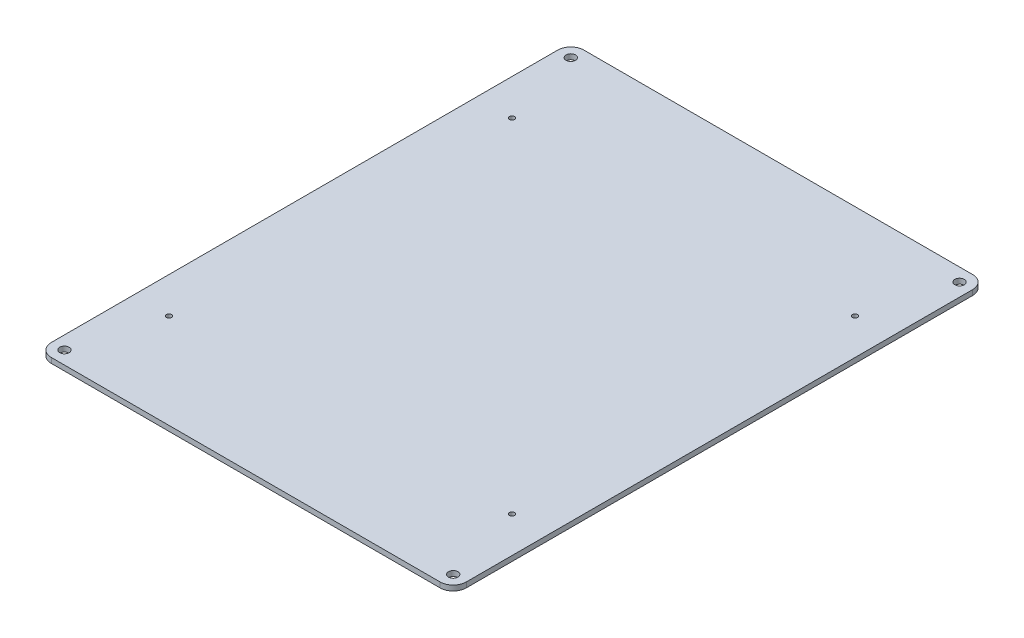
SolidWorks part; units mm, degrees
material "5052-H32"
ref_plane "Front Plane" through (0, 0, 0) normal (0, 0, 1) x (1, 0, 0)
ref_plane "Top Plane" through (0, 0, 0) normal (0, 1, 0) x (1, 0, 0)
ref_plane "Right Plane" through (0, 0, 0) normal (1, 0, 0) x (0, 0, -1)
sketch "Sketch1" plane through (0, 0, 0) normal (0, 1, 0) x (1, 0, 0)
  line L1 (127, 163) -> (-127, 163)
  line L2 (127, 163) -> (127, -163)
  line L3 (127, -163) -> (-127, -163)
  line L4 (-127, 163) -> (-127, -163)
  line L5 (0, -163) -> (0, 163) construction
  line L6 (127, 0) -> (-127, 0) construction
  point P0 (0, 0)
  dimension "D1" = 254
  dimension "D2" = 326
extrude "Boss-Extrude1" add sketch "Sketch1" along normal blind 3.175
sketch "Sketch2" plane through (0, 3.175, 0) normal (0, 1, 0) x (1, 0, 0)
  line L1 (105, 105) -> (-105, 105) construction
  line L2 (105, 105) -> (105, -105) construction
  line L3 (105, -105) -> (-105, -105) construction
  line L4 (-105, 105) -> (-105, -105) construction
  line L5 (0, -105) -> (0, 105) construction
  line L6 (105, 0) -> (-105, 0) construction
  point P4 (-105, 105)
  point P6 (-105, -105)
  point P7 (105, -105)
  point P8 (105, 105)
  dimension "D1" = 210
  dimension "D2" = 210
hole_wizard "M2.5 Clearance Hole1" positions "3DSketch1" profile "Sketch3" hole size "M2.5" standard "ANSI Metric"
sketch3d "3DSketch1"
  point P0 (-105, 3.175, 105)
  point P3 (-105, 3.175, -105)
  point P6 (105, 3.175, -105)
  point P9 (105, 3.175, 105)
sketch "Sketch3" plane through (-105, 3.175, 105) normal (1, 0, 0) x (0, 0, 1)
  line L0 (0, 0) -> (0, 12.8693)
  line L1 (0, 12.8693) -> (1.55, 11.938)
  line L2 (1.55, 11.938) -> (1.55, 0)
  line L5 (1.55, 0) -> (0, 0)
  line L10 (0, 12.8693) -> (-1.55, 11.938) construction
  line L11 (0, -6.35) -> (0, 107.95) construction
  dimension "Hole Dia." = 3.1
  dimension "Hole Depth" = 11.938
  dimension "Drill Angle" = 118
hole_wizard "M5 Clearance Hole1" positions "Sketch5" profile "Sketch4" hole size "M5" standard "ANSI Metric"
sketch "Sketch5" plane through (0, 3.175, 0) normal (0, 1, 0) x (1, 0, 0)
  line L0 (-119, 155) -> (119, -155) construction
  point P0 (-119, 155)
  point P2 (119, 155)
  point P4 (119, -155)
  point P6 (-119, -155)
  dimension "D1" = 238
  dimension "D2" = 310
sketch "Sketch4" plane through (-119, 3.175, -155) normal (1, 0, 0) x (0, 0, 1)
  line L0 (0, 0) -> (0, 13.6805)
  line L1 (0, 13.6805) -> (2.9, 11.938)
  line L2 (2.9, 11.938) -> (2.9, 0)
  line L5 (2.9, 0) -> (0, 0)
  line L10 (0, 13.6805) -> (-2.9, 11.938) construction
  line L11 (0, -6.35) -> (0, 107.95) construction
  dimension "Hole Dia." = 5.8
  dimension "Hole Depth" = 11.938
  dimension "Drill Angle" = 118
fillet "Fillet1" radius 8 4 edges at (127, 1.5875, -163) (-127, 1.5875, -163) (-127, 1.5875, 163) (127, 1.5875, 163)
sketch "Sketch6" plane through (0, 0, 0) normal (0, -1, 0) x (1, 0, 0)
  line L0 (-119, 163) -> (-342.6068, 163)
  line L1 (119, -163) -> (111.8034, -163)
  line L38 (127, -155) -> (127, -135)
  line L39 (127, -135) -> (119, -135)
  line L40 (119, -135) -> (119, -145)
  line L41 (119, -145) -> (115, -145)
  line L42 (115, -145) -> (115, -135)
  line L43 (115, -135) -> (108.5, -135)
  line L44 (108.5, -135) -> (108.5, 135)
  line L45 (108.5, 135) -> (115, 135)
  line L46 (115, 135) -> (115, 145)
  line L47 (115, 145) -> (119, 145)
  line L48 (119, 145) -> (119, 135)
  line L49 (119, 135) -> (127, 135)
  line L50 (127, 135) -> (127, 155)
  line L55 (-127, 155) -> (-127, 135)
  line L56 (-127, 135) -> (-119, 135)
  line L57 (-119, 135) -> (-119, 145)
  line L58 (-119, 145) -> (-115, 145)
  line L59 (-115, 145) -> (-115, 135)
  line L60 (-115, 135) -> (-108.5, 135)
  line L61 (-108.5, 135) -> (-108.5, -135)
  line L62 (-108.5, -135) -> (-115, -135)
  line L63 (-115, -135) -> (-115, -145)
  line L64 (-115, -145) -> (-119, -145)
  line L65 (-119, -145) -> (-119, -135)
  line L66 (-119, -135) -> (-127, -135)
  line L67 (-127, -135) -> (-127, -155)
  line L134 (-119, -163) -> (119, -163)
  line L136 (119, 163) -> (-119, 163)
  arc A13 (119, -163) -> (127, -155) centre (119, -155) ccw
  arc A14 (127, 155) -> (119, 163) centre (119, 155) ccw
  arc A18 (-119, 163) -> (-127, 155) centre (-119, 155) ccw
  arc A19 (-127, -155) -> (-119, -163) centre (-119, -155) ccw
  dimension "D1" = 0
extrude "Cut-Extrude2" [suppressed] cut sketch "Sketch6" against normal blind 10
sketch "Sketch7" plane through (0, 3.175, 0) normal (0, 1, 0) x (1, 0, 0)
  line L0 (0, 0) -> (0, -50000) construction
  line L1 (-127, 155) -> (-127, -155) construction
  line L2 (-127, 135) -> (-112, 135)
  line L3 (-127, 135) -> (-127, -135)
  line L4 (-127, -135) -> (-112, -135)
  line L5 (-112, 135) -> (-112, -135)
  line L6 (-119.5, -135) -> (-119.5, 135) construction
  line L7 (-127, 0) -> (-112, 0) construction
  line L8 (127, 0) -> (112, 0) construction
  line L9 (119.5, -135) -> (119.5, 135) construction
  line L10 (112, 135) -> (112, -135)
  line L11 (127, -135) -> (112, -135)
  line L12 (127, 135) -> (127, -135)
  line L13 (127, 135) -> (112, 135)
  point P17 (119.5, 0)
  point P151 (-119.5, 0)
  dimension "D1" = 270
  dimension "D2" = 15
extrude "Cut-Extrude3" [suppressed] cut sketch "Sketch7" against normal blind 10
